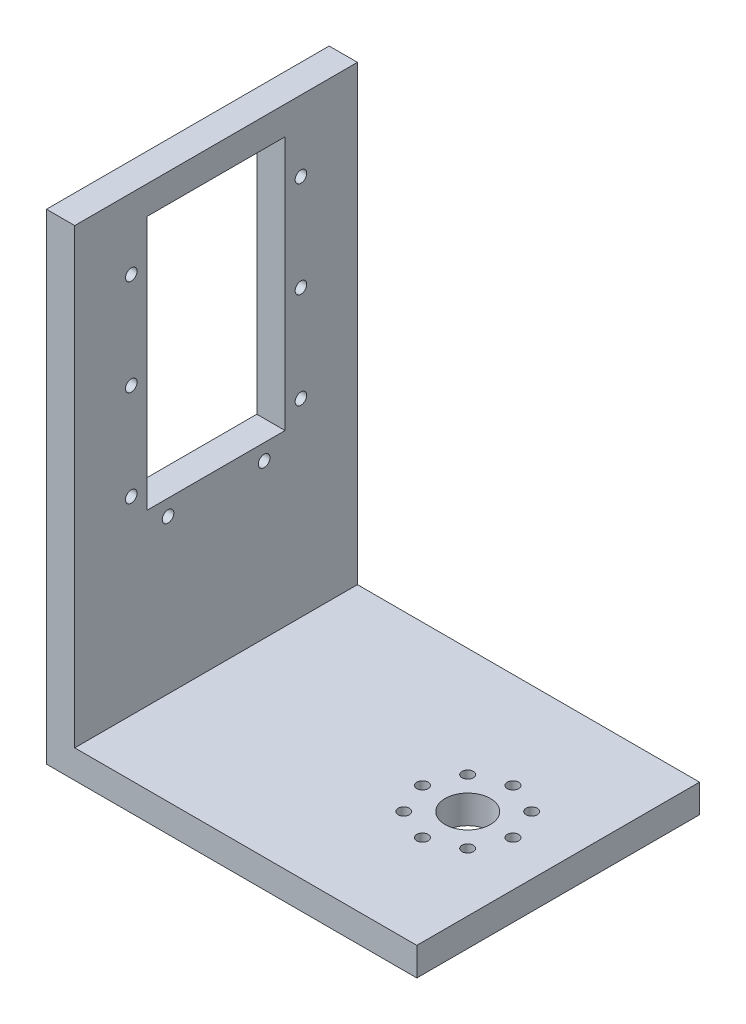
SolidWorks part; units mm, degrees
material "ABS"
ref_plane "Front Plane" through (0, 0, 0) normal (0, 0, 1) x (1, 0, 0)
ref_plane "Top Plane" through (0, 0, 0) normal (0, 1, 0) x (1, 0, 0)
ref_plane "Right Plane" through (0, 0, 0) normal (1, 0, 0) x (0, 0, -1)
sketch "Sketch1" plane through (0, 0, 0) normal (0, 1, 0) x (1, 0, 0)
  line L0 (65.5, 25) -> (49.5, 25) construction
  line L1 (0, 0) -> (65.5, 0)
  line L2 (0, 0) -> (0, 50)
  line L3 (0, 50) -> (65.5, 50)
  line L4 (65.5, 0) -> (65.5, 50)
  line L5 (49.5, 33) -> (49.5, 25) construction
  circle A0 centre (49.5, 25) radius 4
  circle A1 centre (49.5, 33) radius 1
  circle A2 centre (55.1569, 30.6569) radius 1
  circle A3 centre (57.5, 25) radius 1
  circle A4 centre (55.1569, 19.3431) radius 1
  circle A5 centre (49.5, 17) radius 1
  circle A6 centre (43.8431, 19.3431) radius 1
  circle A7 centre (41.5, 25) radius 1
  circle A8 centre (43.8431, 30.6569) radius 1
  point P26 (49.5, 25)
  dimension "D3" = 8
  dimension "D5" = 2
  dimension "D1" = 65.5
  dimension "D2" = 50
  dimension "D4" = 16
  dimension "D7" = 8
  dimension "D6" = 8
extrude "Boss-Extrude1" add sketch "Sketch1" along normal blind 5
sketch "Sketch3" plane through (0, 0, 0) normal (0, 1, 0) x (1, 0, 0)
  line L0 (65.5, 50) -> (0, 50) construction
  line L1 (0, 0) -> (5, 0)
  line L2 (0, 0) -> (0, 50)
  line L3 (0, 50) -> (5, 50)
  line L4 (5, 0) -> (5, 50)
  dimension "D1" = 5
extrude "Boss-Extrude2" add sketch "Sketch3" along normal blind 85
sketch "Sketch4" plane through (0, 0, 0) normal (-1, 0, 0) x (0, 0, 1)
  line L0 (-25, 85) -> (-25, 23.7384) construction
  line L1 (-50, 85) -> (0, 85) construction
  line L2 (-40, 72.5) -> (-10, 72.5) construction
  line L3 (-37.2, 35) -> (-12.8, 35)
  line L4 (-37.2, 35) -> (-37.2, 80)
  line L5 (-37.2, 80) -> (-12.8, 80)
  line L6 (-12.8, 35) -> (-12.8, 80)
  line L7 (-40, 55.5) -> (-10, 55.5) construction
  line L9 (-40, 38.5) -> (-33.5, 32.2) construction
  line L10 (-40, 55.5) -> (-40, 38.5) construction
  circle A0 centre (-40, 72.5) radius 1.025
  circle A1 centre (-10, 72.5) radius 1.025
  circle A2 centre (-40, 55.5) radius 1.025
  circle A3 centre (-40, 38.5) radius 1.025
  circle A5 centre (-10, 55.5) radius 1.025
  circle A6 centre (-33.5, 32.2) radius 1.025
  circle A8 centre (-16.5, 32.2) radius 1.025
  circle A9 centre (-10, 38.5) radius 1.025
  point P8 (-25, 80)
  point P9 (-25, 80)
  point P12 (-25, 72.5)
  dimension "D4" = 2.05
  dimension "D1" = 24.4
  dimension "D2" = 45
  dimension "D3" = 30
  dimension "D5" = 17
  dimension "D6" = 7.5
  dimension "D7" = 17
  dimension "D8" = 6.5
  dimension "D9" = 6.3
  dimension "D10" = 5
extrude "Cut-Extrude1" cut sketch "Sketch4" against normal through all
